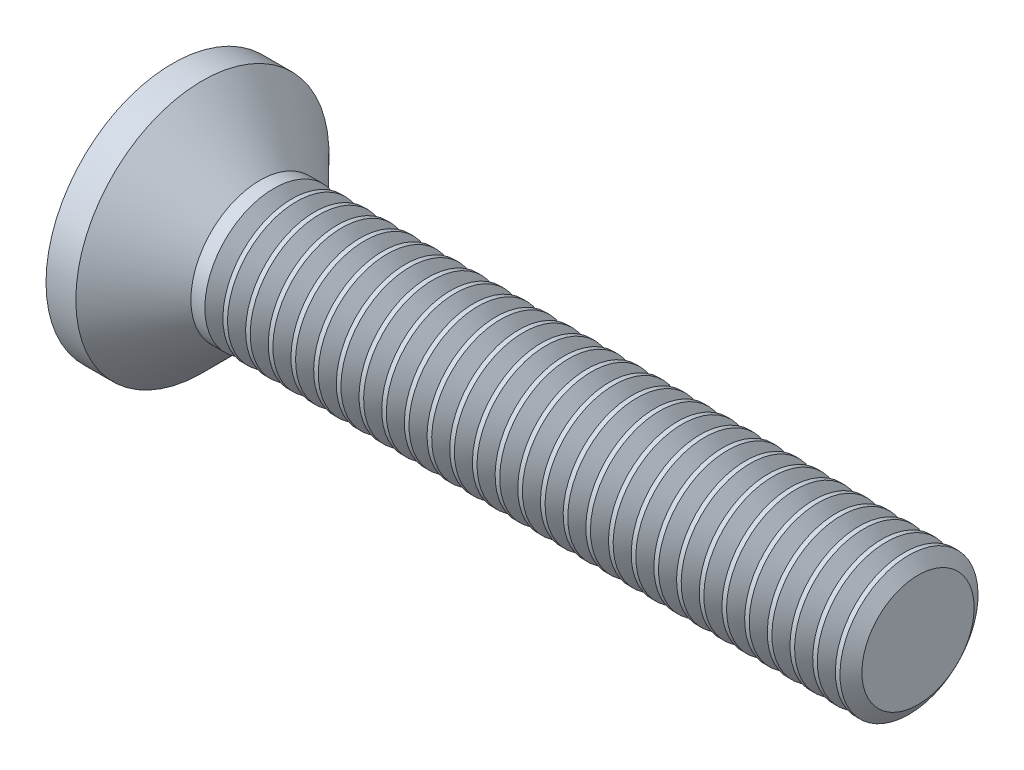
SolidWorks part; units mm, degrees
revolve "Base-Revolve" add sketch "BodySke" angle 360 about L4
sketch "BodySke" plane through (0, 0, 0) normal (0, 0, 1) x (1, 0, 0)
  line L0 (0, 0) -> (16.7277, 0)
  line L1 (16.7277, 0) -> (16.7277, 1.5)
  line L2 (16.7277, 1.5) -> (2.4277, 1.5)
  line L3 (2.4277, 1.5) -> (-7.1953, 11.123) construction
  line L4 (-15.875, 0) -> (82.55, 0) construction
  line L5 (2.4277, -1.5) -> (-7.1953, -11.123) construction
  line L6 (2.9277, 4.675) -> (2.9277, -11.2) construction
  line L7 (0.7277, 8.7375) -> (0.7277, -7.1375) construction
  line L8 (2.4277, 1.5) -> (1.1777, 2.75)
  line L9 (1.1777, 2.75) -> (0.53, 2.75)
  arc A0 (0, 0) -> (0.53, 2.75) centre (7.4, 0) cw
  arc A1 (0.7277, 3.2) -> (0, 0) centre (7.4, 0) ccw construction
  dimension "Crown_rad" = 7.4
  dimension "Diameter" = 3
  dimension "Advance" = 0.5
  dimension "Head_ang" = 90
  dimension "D3" = 6.4
  dimension "Side_ht" = 1.7
  dimension "D4" = 0.7277
  dimension "Head_dia" = 5.5
cosmetic thread "ThreadCosmetic" [suppressed] parameters "Thread_length"=2.8, "Thread_minor"=2.439
ref_plane "Plane1" through (0, 0, 0) normal (0, 0, 1) x (1, 0, 0)
ref_plane "Plane2" through (0, 0, 0) normal (0, 1, 0) x (1, 0, 0)
ref_plane "Plane3" through (0, 0, 0) normal (1, 0, 0) x (0, 0, -1)
sketch "Sketch2" plane through (0, 0, 0) normal (1, 0, 0) x (0, 0, -1)
  line L0 (2.75, -0.5) -> (-2.75, -0.5)
  line L1 (2.75, -0.5) -> (2.75, 0.5)
  line L2 (-2.75, 0.5) -> (2.75, 0.5)
  line L3 (-2.75, 0.5) -> (-2.75, -0.5)
  dimension "D1" = 5.5
  dimension "Slot_width" = 1
  dimension "D3" = 2.75
  dimension "D4" = 0.5
extrude "Slot" [suppressed] cut sketch "Sketch2" along normal blind 1.5
sketch "Sketch3" plane through (0, 0, 0) normal (1, 0, 0) x (0, 0, -1)
  line L0 (0.415, -1.72) -> (-0.415, -1.72)
  line L1 (0.415, -1.72) -> (0.415, 1.72)
  line L2 (-0.415, 1.72) -> (0.415, 1.72)
  line L3 (-0.415, 1.72) -> (-0.415, -1.72)
  dimension "Cross_width" = 0.83
  dimension "D1" = 0.415
  dimension "Cross_dia" = 3.44
  dimension "D2" = 1.72
ref_plane "Plane4" through (2.33, 0, 0) normal (1, 0, 0) x (0, 0, -1)
sketch "Sketch4" plane through (2.33, 0, 0) normal (1, 0, 0) x (0, 0, -1)
  line L0 (0.2075, -0.2075) -> (-0.2075, -0.2075)
  line L1 (0.2075, -0.2075) -> (0.2075, 0.2075)
  line L2 (-0.2075, 0.2075) -> (0.2075, 0.2075)
  line L3 (-0.2075, 0.2075) -> (-0.2075, -0.2075)
  dimension "D1" = 0.415
  dimension "D2" = 0.415
  dimension "D3" = 0.2075
  dimension "D4" = 0.2075
loft "Cross" cut profiles "Sketch3", "Sketch4"
pattern_circular "CirPattern1" count 2 every 90 about axis through (0, 0, 0) along (1, 0, 0) of "Cross"
sketch "ThdSchSke" plane through (0, 0, 0) normal (0, 0, 1) x (1, 0, 0)
  line L0 (2.9277, -1.2195) -> (2.7313, -1.5)
  line L1 (2.9277, -1.2195) -> (3.1241, -1.5)
  line L2 (3.1241, -1.5) -> (3.1241, -1.875)
  line L3 (-3.175, 0) -> (5.1513, 0) construction
  line L5 (3.1241, -1.875) -> (2.7313, -1.875)
  line L6 (2.7313, -1.875) -> (2.7313, -1.5)
  line L8 (16.7277, -1.5) -> (16.7277, 1.5) construction
  dimension "Diameter" = 3
  dimension "Thread_minor" = 2.439
  dimension "Start" = 2.8
revolve "ThreadSchematic" cut sketch "ThdSchSke" angle 360 about L3
pattern_linear "ThdSchPat" count 29 spacing 0.4929 along (1, 0, 0) of "ThreadSchematic"
equation "\"D1@Sketch2\" = \"Head_dia@BodySke\""
equation "\"D3@Sketch2\" = \"D1@Sketch2\" / 2"
equation "\"D4@Sketch2\" = \"Slot_width@Sketch2\" / 2"
equation "\"D1@Sketch3\" = \"Cross_width@Sketch3\" / 2"
equation "\"D2@Sketch3\" = \"Cross_dia@Sketch3\" / 2"
equation "\"D1@Sketch4\" = \"Cross_width@Sketch3\"*.5"
equation "\"D2@Sketch4\" = \"D1@Sketch4\""
equation "\"D3@Sketch4\" = \"D1@Sketch4\" / 2"
equation "\"D4@Sketch4\" = \"D2@Sketch4\" / 2"
equation "\"Thread_length@ThreadCosmetic\" = ((sgn( (\"Length@BodySke\" - \"Advance@BodySke\" - \"Side_ht@BodySke\" ) - \"Thread_nom@BodySke\" )-1)*( (\"Length@BodySke\" - \"Advance@BodySke\" - \"Side_ht@BodySke\" ) - \"Thread_nom@BodySke\" ))/-2+ \"Thread_nom@BodySke\""
equation "\"Thread_minor@ThdSchSke\" = \"Thread_minor@ThreadCosmetic\""
equation "\"Diameter@ThdSchSke\" = \"Diameter@BodySke\""
equation "\"Overcut@ThdSchSke\" = \"Diameter@BodySke\" * 1.25"
equation "\"Start@ThdSchSke\" =  \"Thread_length@ThreadCosmetic\""
equation "\"Num_threads@ThdSchPat\" = int( \"Thread_length@ThreadCosmetic\" / \"Advance@BodySke\" + 0.999 )  + 1"
equation "\"Advance@ThdSchPat\" = \"Thread_length@ThreadCosmetic\" /  (\"Num_threads@ThdSchPat\" - 1) 'relax it"
